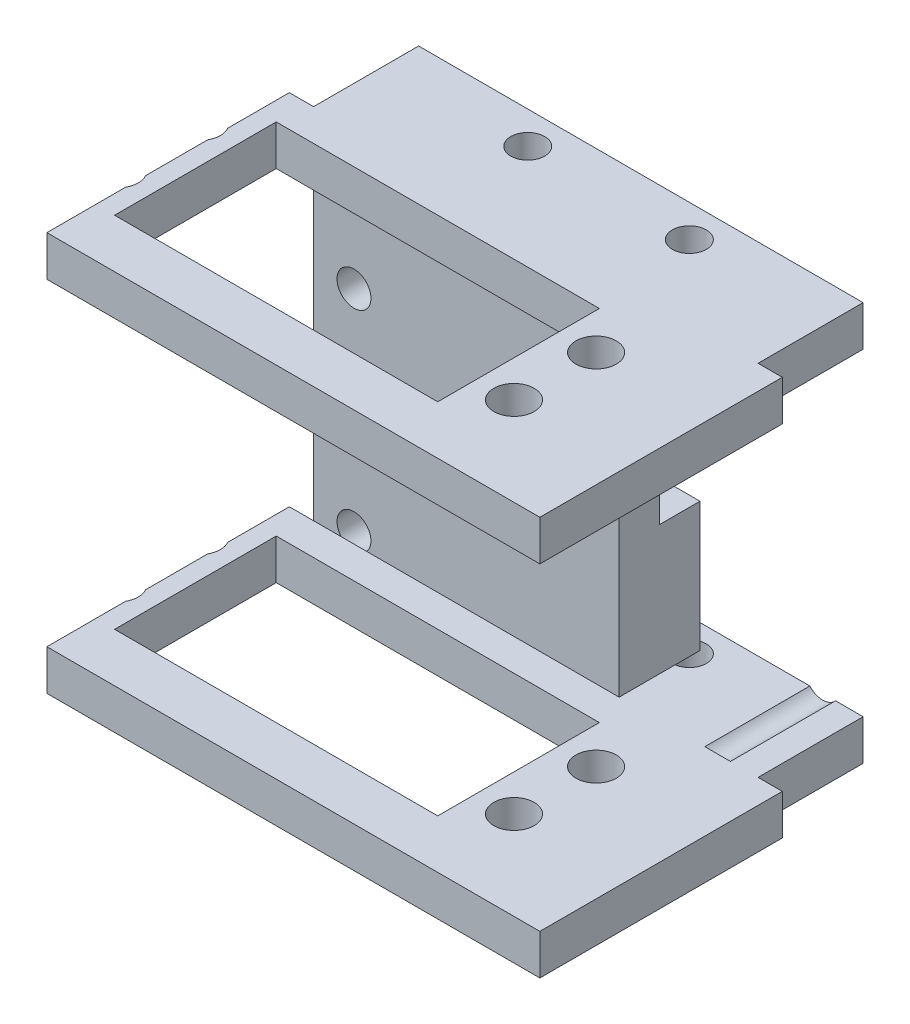
SolidWorks part; units mm, degrees
ref_plane "Front Plane" through (0, 0, 0) normal (0, 0, 1) x (1, 0, 0)
ref_plane "Top Plane" through (0, 0, 0) normal (0, 1, 0) x (1, 0, 0)
ref_plane "Right Plane" through (0, 0, 0) normal (1, 0, 0) x (0, 0, -1)
sketch "Sketch1" plane through (0, 0, 0) normal (0, 0, 1) x (1, 0, 0)
  line L0 (16.3907, 6.2797) -> (19.8282, 6.2797)
  line L1 (13.6407, 17.2797) -> (13.6407, 9.0297)
  line L2 (-17.9843, 6.2797) -> (-14.5468, 6.2797)
  line L3 (-11.7968, 9.0297) -> (-11.7968, 17.2797)
  line L4 (19.8282, -6.0953) -> (16.3907, -6.0953)
  line L5 (13.6407, -8.8453) -> (13.6407, -22.0953)
  line L6 (-11.7968, -17.0953) -> (-11.7968, -3.8453)
  line L7 (-14.5468, -1.0953) -> (-17.9843, -1.0953)
  line L8 (-11.7968, -17.0953) -> (-17.9843, -17.0953)
  line L9 (-17.9843, -1.0953) -> (-17.9843, -17.0953)
  line L10 (19.8282, -22.0953) -> (19.8282, -6.0953)
  line L11 (19.8282, -22.0953) -> (13.6407, -22.0953)
  line L12 (19.8282, 6.2797) -> (19.8282, 17.2797)
  line L13 (13.6407, 17.2797) -> (19.8282, 17.2797)
  line L14 (-17.9843, 17.2797) -> (-11.7968, 17.2797)
  line L15 (-17.9843, 17.2797) -> (-17.9843, 6.2797)
  arc A0 (13.6407, 9.0297) -> (16.3907, 6.2797) centre (16.3907, 9.0297) ccw
  arc A1 (-14.5468, 6.2797) -> (-11.7968, 9.0297) centre (-14.5468, 9.0297) ccw
  arc A2 (16.3907, -6.0953) -> (13.6407, -8.8453) centre (16.3907, -8.8453) ccw
  arc A3 (-11.7968, -3.8453) -> (-14.5468, -1.0953) centre (-14.5468, -3.8453) ccw
  dimension "D1" = 16
  dimension "D2" = 11
  dimension "D3" = 11
  dimension "D4" = 16
extrude "Boss-Extrude1" add sketch "Sketch1" along normal blind 5
sketch "Sketch2" plane through (0, 0, 5) normal (0, 0, 1) x (1, 0, 0)
  line L1 (-17.9843, 17.2797) -> (19.8282, 17.2797)
  line L2 (-17.9843, 17.2797) -> (-17.9843, -22.0953)
  line L3 (-17.9843, -22.0953) -> (19.8282, -22.0953)
  line L4 (19.8282, 17.2797) -> (19.8282, -22.0953)
  line L5 (-17.9843, 17.2797) -> (19.8282, -22.0953) construction
  line L6 (-17.9843, -22.0953) -> (19.8282, 17.2797) construction
  point P4 (0.9219, -2.4078)
extrude "Boss-Extrude2" add sketch "Sketch2" along normal blind 5
sketch "Sketch3" plane through (0, 17.2797, 0) normal (0, 1, 0) x (1, 0, 0)
  line L0 (37.0157, 0) -> (37.0157, 12) construction
  line L1 (-17.9843, -10) -> (37.0157, -10)
  line L2 (-17.9843, -10) -> (-17.9843, 3)
  line L3 (-17.9843, 3) -> (37.0157, 3)
  line L4 (37.0157, -10) -> (37.0157, 3)
  line L5 (-17.9843, -10) -> (37.0157, 3) construction
  line L6 (-17.9843, 3) -> (37.0157, -10) construction
  line L7 (3.0157, 3) -> (-3.9843, 3) construction
  circle A0 centre (-0.4843, -1) radius 2.1
  circle A1 centre (19.5157, -1) radius 2.1
  point P4 (9.5157, -3.5)
extrude "Boss-Extrude3" add sketch "Sketch3" along normal blind 5
ref_plane "Plane1" through (0, -2.4078, 0) normal (0, -1, 0) x (-1, 0, 0)
mirror "Mirror1" about plane through (0, -2.4078, 0) normal (0, -1, 0) of "Boss-Extrude3"
sketch "Sketch4" plane through (0, 22.2797, 0) normal (0, 1, 0) x (1, 0, 0)
  line L0 (-17.9843, 3) -> (-17.9843, -10) construction
  line L1 (-20.9843, -10) -> (40.0157, -10)
  line L2 (-20.9843, -10) -> (-20.9843, -40)
  line L3 (-20.9843, -40) -> (40.0157, -40)
  line L4 (40.0157, -10) -> (40.0157, -40)
  line L5 (-20.9843, -10) -> (40.0157, -40) construction
  line L6 (-20.9843, -40) -> (40.0157, -10) construction
  line L7 (37.0157, -10) -> (37.0157, 3) construction
  point P4 (9.5157, -25)
  dimension "D1" = 30
  dimension "D2" = 3
  dimension "D3" = 3
extrude "Boss-Extrude4" add sketch "Sketch4" against normal blind 5
mirror "Mirror2" about plane through (0, -2.4078, 0) normal (0, -1, 0) of "Boss-Extrude4"
sketch "Sketch5" plane through (0, 17.2797, 0) normal (0, -1, 0) x (1, 0, 0)
  line L0 (-24.709, 33.9459) -> (-17.659, 33.9459) construction
  line L1 (-18.659, 33.9459) -> (21.3242, 33.9459)
  line L2 (-18.659, 33.9459) -> (-18.659, 13.9459)
  line L3 (-18.659, 13.9459) -> (21.3242, 13.9459)
  line L4 (21.3242, 33.9459) -> (21.3242, 13.9459)
  line L5 (-18.659, 33.9459) -> (21.3242, 13.9459) construction
  line L6 (-18.659, 13.9459) -> (21.3242, 33.9459) construction
  line L7 (27.391, 13.9459) -> (20.341, 13.9459) construction
  circle A0 centre (-23.159, 29.0259) radius 2.5
  circle A1 centre (-23.159, 18.8659) radius 2.5
  circle A2 centre (25.841, 29.0259) radius 2.5
  circle A3 centre (25.841, 18.8659) radius 2.5
  point P16 (1.3326, 23.9459)
extrude "Cut-Extrude3" cut sketch "Sketch5" against normal blind 5
sketch "Sketch7" plane through (0, 0, 10) normal (0, 0, 1) x (1, 0, 0)
  circle A0 centre (32.0157, -20.7203) radius 2.1
  circle A1 centre (-12.9843, -20.7203) radius 2.1
  circle A2 centre (32.0157, 5.2797) radius 2.1
  circle A3 centre (-12.9843, 5.2797) radius 2.1
extrude "Cut-Extrude4" cut sketch "Sketch7" against normal through all
mirror "Mirror3" about plane through (0, -2.4078, 0) normal (0, -1, 0) of "Cut-Extrude3"
